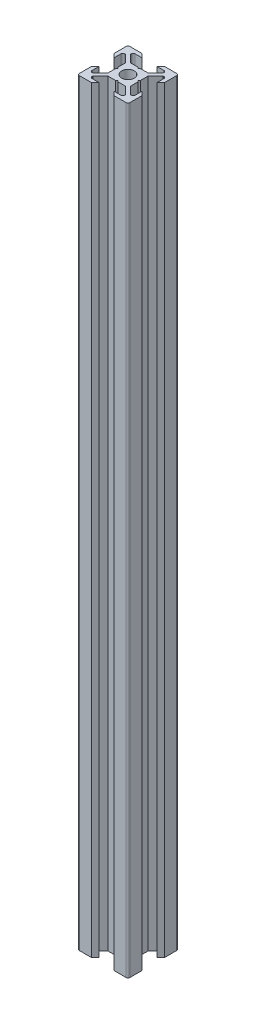
SolidWorks part; units mm, degrees
ref_plane "Face" through (0, 0, 0) normal (0, 0, 1) x (1, 0, 0)
ref_plane "Dessus" through (0, 0, 0) normal (0, 1, 0) x (1, 0, 0)
ref_plane "Droite" through (0, 0, 0) normal (1, 0, 0) x (0, 0, -1)
sketch "Esquisse1" plane through (0, 0, 0) normal (0, 1, 0) x (1, 0, 0)
  line L0 (0, 0) -> (0, 10) construction
  line L1 (0, 0) -> (-10, 0) construction
  line L2 (-10, 0) -> (-10, 10) construction
  line L3 (-10, 10) -> (0, 10) construction
  line L4 (0, 4) -> (-0.5, 4.5)
  line L5 (-0.5, 4.5) -> (-3.4393, 4.5)
  line L6 (-3.4393, 4.5) -> (-6.4393, 7.5)
  line L7 (-6.4393, 7.5) -> (-6.4393, 8.5)
  line L8 (-6.4393, 8.5) -> (-3, 8.5)
  line L9 (-3, 8.5) -> (-4.5, 10)
  line L10 (-4.5, 10) -> (-10, 10)
  line L11 (0, 0) -> (-10, 10) construction
  line L12 (-10, 4.5) -> (-10, 10)
  line L13 (-8.5, 3) -> (-10, 4.5)
  line L14 (-8.5, 6.4393) -> (-8.5, 3)
  line L15 (-7.5, 6.4393) -> (-8.5, 6.4393)
  line L16 (-4.5, 3.4393) -> (-7.5, 6.4393)
  line L17 (-4.5, 0.5) -> (-4.5, 3.4393)
  line L18 (-4, 0) -> (-4.5, 0.5)
  line L19 (0, -4) -> (-0.5, -4.5)
  line L20 (-0.5, -4.5) -> (-3.4393, -4.5)
  line L21 (-4, 0) -> (-4.5, -0.5)
  line L22 (-4.5, -0.5) -> (-4.5, -3.4393)
  line L23 (-4.5, -3.4393) -> (-7.5, -6.4393)
  line L24 (-3.4393, -4.5) -> (-6.4393, -7.5)
  line L25 (-3, -8.5) -> (-4.5, -10)
  line L26 (-6.4393, -8.5) -> (-3, -8.5)
  line L27 (-6.4393, -7.5) -> (-6.4393, -8.5)
  line L28 (-7.5, -6.4393) -> (-8.5, -6.4393)
  line L29 (-4.5, -10) -> (-10, -10)
  line L30 (-10, -4.5) -> (-10, -10)
  line L31 (-8.5, -3) -> (-10, -4.5)
  line L32 (-8.5, -6.4393) -> (-8.5, -3)
  line L33 (8.5, -6.4393) -> (8.5, -3)
  line L34 (8.5, -3) -> (10, -4.5)
  line L35 (10, -4.5) -> (10, -10)
  line L36 (4.5, -10) -> (10, -10)
  line L37 (7.5, -6.4393) -> (8.5, -6.4393)
  line L38 (6.4393, -7.5) -> (6.4393, -8.5)
  line L39 (6.4393, -8.5) -> (3, -8.5)
  line L40 (3, -8.5) -> (4.5, -10)
  line L41 (3.4393, -4.5) -> (6.4393, -7.5)
  line L42 (4.5, -3.4393) -> (7.5, -6.4393)
  line L43 (4.5, -0.5) -> (4.5, -3.4393)
  line L44 (4, 0) -> (4.5, -0.5)
  line L45 (0.5, -4.5) -> (3.4393, -4.5)
  line L46 (0, -4) -> (0.5, -4.5)
  line L47 (4, 0) -> (4.5, 0.5)
  line L48 (4.5, 0.5) -> (4.5, 3.4393)
  line L49 (4.5, 3.4393) -> (7.5, 6.4393)
  line L50 (7.5, 6.4393) -> (8.5, 6.4393)
  line L51 (8.5, 6.4393) -> (8.5, 3)
  line L52 (8.5, 3) -> (10, 4.5)
  line L53 (10, 4.5) -> (10, 10)
  line L54 (4.5, 10) -> (10, 10)
  line L55 (3, 8.5) -> (4.5, 10)
  line L56 (6.4393, 8.5) -> (3, 8.5)
  line L57 (6.4393, 7.5) -> (6.4393, 8.5)
  line L58 (3.4393, 4.5) -> (6.4393, 7.5)
  line L59 (0.5, 4.5) -> (3.4393, 4.5)
  line L60 (0, 4) -> (0.5, 4.5)
  circle A0 centre (0, 0) radius 2.5
  dimension "D10" = 5
  dimension "D1" = 10
  dimension "D2" = 45
  dimension "D3" = 45
  dimension "D4" = 1.5
  dimension "D5" = 7
  dimension "D6" = 1
  dimension "D7" = 4.5
  dimension "D8" = 0.5
  dimension "D9" = 0.75
extrude "Extrusion1" add sketch "Esquisse1" along normal blind 300
fillet "Congé1" radius 0.75 12 edges at (-8.5, 150, -6.4393) (-6.4393, 150, -8.5) (8.5, 150, -6.4393) (6.4393, 150, -8.5) (-8.5, 150, 6.4393) (-6.4393, 150, 8.5) (8.5, 150, 6.4393) (6.4393, 150, 8.5) (10, 150, -10) (-10, 150, -10) (-10, 150, 10) (10, 150, 10)
